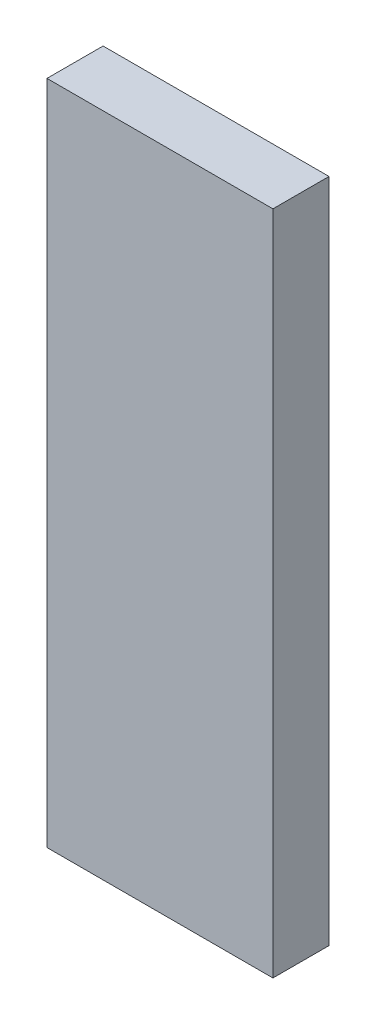
SolidWorks part; units mm, degrees
ref_plane "Front Plane" through (0, 0, 0) normal (0, 0, 1) x (1, 0, 0)
ref_plane "Top Plane" through (0, 0, 0) normal (0, 1, 0) x (1, 0, 0)
ref_plane "Right Plane" through (0, 0, 0) normal (1, 0, 0) x (0, 0, -1)
sketch "Sketch1" plane through (0, 0, 0) normal (0, 1, 0) x (1, 0, 0)
  line L0 (-14.5, -3.6) -> (14.5, 3.6) construction
  line L1 (-14.5, 3.6) -> (14.5, 3.6)
  line L2 (-14.5, 3.6) -> (-14.5, -3.6)
  line L3 (-14.5, -3.6) -> (14.5, -3.6)
  line L4 (14.5, 3.6) -> (14.5, -3.6)
  point P4 (0, 0)
  dimension "D1" = 7.2
  dimension "D2" = 29
extrude "Boss-Extrude1" add sketch "Sketch1" along normal blind 85.5
